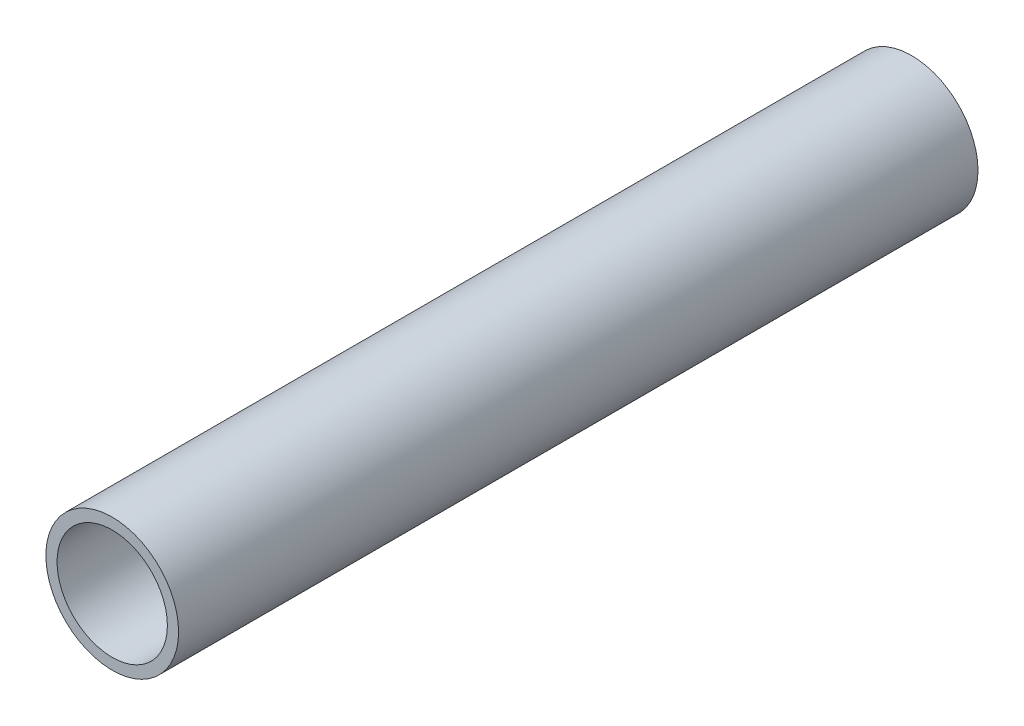
SolidWorks part; units mm, degrees
ref_plane "Front Plane" through (0, 0, 0) normal (0, 0, 1) x (1, 0, 0)
ref_plane "Top Plane" through (0, 0, 0) normal (0, 1, 0) x (1, 0, 0)
ref_plane "Right Plane" through (0, 0, 0) normal (1, 0, 0) x (0, 0, -1)
sketch "Sketch1" plane through (0, 0, 0) normal (0, 0, 1) x (1, 0, 0)
  circle A0 centre (0, 0) radius 21.082
  dimension "Pipe OD" = 42.164
extrude "Extrude-Thin1" add sketch "Sketch1" along normal mid plane 254 thin thin type one direction reverse wall 3.556
